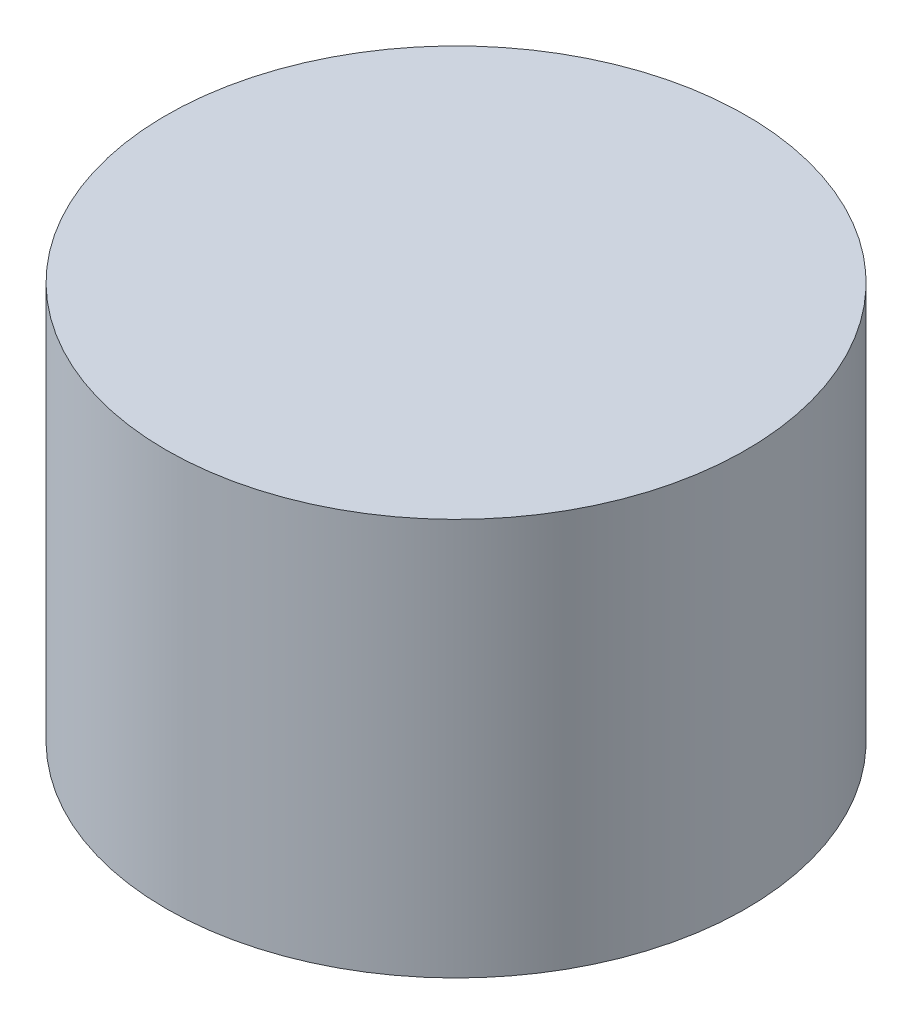
SolidWorks part; units mm, degrees
ref_plane "Front Plane" through (0, 0, 0) normal (0, 0, 1) x (1, 0, 0)
ref_plane "Top Plane" through (0, 0, 0) normal (0, 1, 0) x (1, 0, 0)
ref_plane "Right Plane" through (0, 0, 0) normal (1, 0, 0) x (0, 0, -1)
sketch "Sketch1" plane through (0, 0, 0) normal (0, 1, 0) x (1, 0, 0)
  circle A0 centre (0, 0) radius 0.365
  dimension "D1" = 0.73
extrude "Boss-Extrude1" add sketch "Sketch1" along normal blind 0.5
